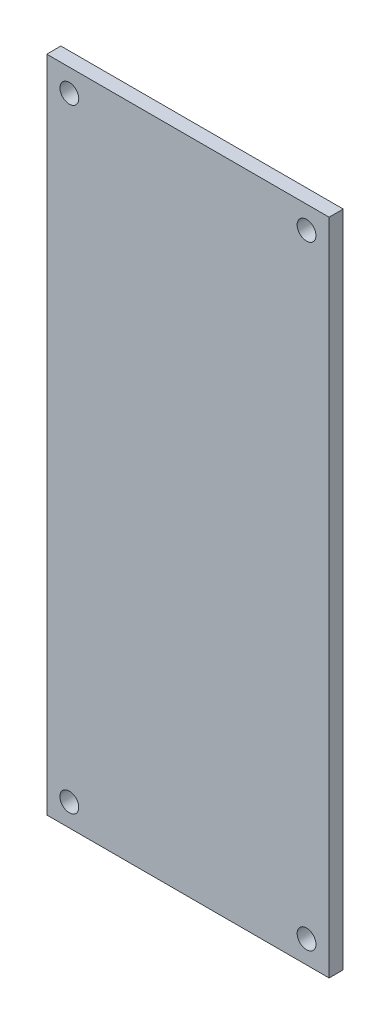
SolidWorks part; units mm, degrees
ref_plane "Спереди" through (0, 0, 0) normal (0, 0, 1) x (1, 0, 0)
ref_plane "Сверху" through (0, 0, 0) normal (0, 1, 0) x (1, 0, 0)
ref_plane "Справа" through (0, 0, 0) normal (1, 0, 0) x (0, 0, -1)
sketch "Sketch1" plane through (0, 0, 0) normal (0, 0, 1) x (1, 0, 0)
  line L0 (0, 35) -> (0, -35) construction
  line L1 (-15, -35) -> (15, -35)
  line L2 (-15, -35) -> (-15, 35)
  line L3 (-15, 35) -> (15, 35)
  line L4 (15, -35) -> (15, 35)
  line L5 (-15, 0) -> (15, 0) construction
  circle A0 centre (-12.6, 32.6) radius 1
  circle A1 centre (12.6, 32.6) radius 1
  circle A2 centre (12.6, -32.6) radius 1
  circle A3 centre (-12.6, -32.6) radius 1
  point P5 (-15, 0)
  point P8 (0, 35)
  dimension "D3" = 2
  dimension "D1" = 70
  dimension "D2" = 30
  dimension "D4" = 2.4
  dimension "D5" = 2.4
extrude "Boss-Extrude1" add sketch "Sketch1" along normal blind 1.5
